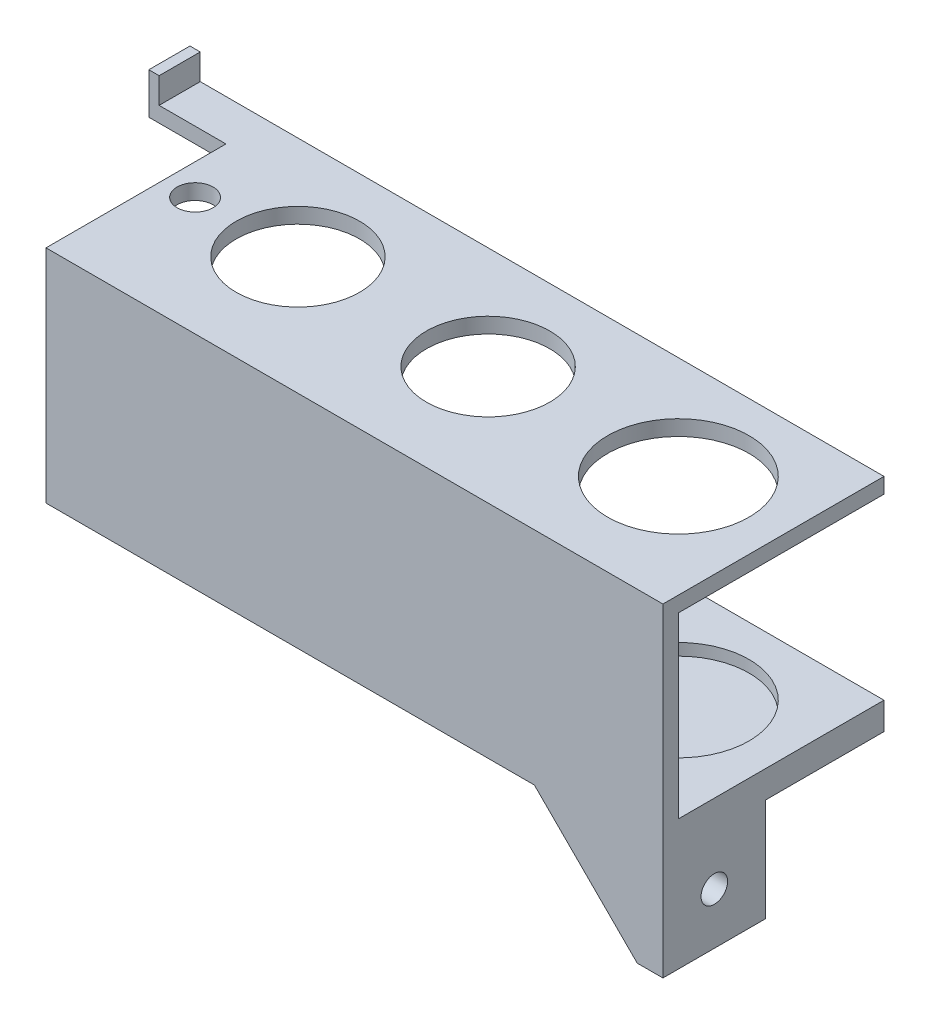
SolidWorks part; units mm, degrees
ref_plane "Front Plane" through (0, 0, 0) normal (0, 0, 1) x (1, 0, 0)
ref_plane "Top Plane" through (0, 0, 0) normal (0, 1, 0) x (1, 0, 0)
ref_plane "Right Plane" through (0, 0, 0) normal (1, 0, 0) x (0, 0, -1)
sketch "Sketch1" plane through (0, 0, 0) normal (1, 0, 0) x (0, 0, -1)
  line L7 (0, -33) -> (3, -33)
  line L8 (3, 7) -> (3, -33)
  line L9 (3, 7) -> (0, 7)
  line L10 (0, 7) -> (0, -33)
  dimension "D4" = 3
  dimension "D5" = 40
extrude "Boss-Extrude1" add sketch "Sketch1" along normal blind 120
sketch "Sketch9" plane through (0, 0, -3) normal (0, 0, -1) x (-1, 0, 0)
  line L0 (0, 7) -> (0, -33) construction
  line L1 (-120, -33) -> (0, -33)
  line L2 (-120, -33) -> (-120, -30)
  line L3 (-120, -30) -> (0, -30)
  line L4 (0, -33) -> (0, -30)
  dimension "D1" = 3
extrude "Boss-Extrude2" add sketch "Sketch9" along normal blind 40
sketch "Sketch10" plane through (0, -30, 0) normal (0, 1, 0) x (1, 0, 0)
  line L0 (120, 43) -> (120, 3) construction
  line L2 (120, 43) -> (0, 43)
  line L3 (120, 43) -> (120, 3)
  line L4 (120, 3) -> (0, 3)
  line L5 (0, 43) -> (0, 3)
  circle A0 centre (100, 23) radius 13.75
  circle A1 centre (63, 23) radius 7.6
  circle A2 centre (26, 23) radius 7.6
  circle A3 centre (6, 23) radius 2.26
  point P5 (120, 23)
  dimension "D1" = 27.5
  dimension "D2" = 20
  dimension "D3" = 15.2
  dimension "D4" = 15.2
  dimension "D5" = 37
  dimension "D6" = 37
  dimension "D7" = 4.52
  dimension "D8" = 20
extrude "Boss-Extrude3" add sketch "Sketch10" along normal blind 2.3
sketch "Sketch11" plane through (0, -30, 0) normal (0, 1, 0) x (1, 0, 0)
  circle A0 centre (63, 23) radius 7
  circle A1 centre (26, 23) radius 2.25
  circle A2 centre (6, 23) radius 2.26
  dimension "D1" = 14
  dimension "D2" = 4.5
extrude "Cut-Extrude5" cut sketch "Sketch11" against normal through all
sketch "Sketch12" plane through (0, 7, 0) normal (0, 1, 0) x (1, 0, 0)
  line L1 (0, 0) -> (120, 0)
  line L2 (0, 0) -> (0, 43)
  line L3 (0, 43) -> (120, 43)
  line L4 (120, 0) -> (120, 43)
  circle A0 centre (6, 23) radius 3.5
  circle A1 centre (26, 23) radius 12
  circle A2 centre (63, 23) radius 12
  circle A3 centre (100, 23) radius 13.75
  circle A4 centre (100, 23) radius 13.75 construction
  dimension "D1" = 24
  dimension "D2" = 24
  dimension "D3" = 7
extrude "Boss-Extrude4" add sketch "Sketch12" along normal blind 3
sketch "Sketch13" plane through (120, 0, 0) normal (1, 0, 0) x (0, 0, -1)
  line L1 (0, -33) -> (20, -33)
  line L2 (0, -33) -> (0, -53)
  line L3 (0, -53) -> (20, -53)
  line L4 (20, -33) -> (20, -53)
  circle A0 centre (10, -43) radius 2.5837
  point P7 (0, 0)
  point P8 (10, -53)
  point P9 (0, 0)
  point P10 (20, -43)
  dimension "D1" = 20
extrude "Boss-Extrude5" add sketch "Sketch13" against normal blind 5
sketch "Sketch14" plane through (0, 0, 0) normal (0, 0, 1) x (1, 0, 0)
  line L0 (115, -53) -> (115, -33)
  line L1 (115, -33) -> (95, -33)
  line L2 (115, -33) -> (0, -33) construction
  line L3 (95, -33) -> (115, -53)
extrude "Boss-Extrude6" add sketch "Sketch14" against normal blind 2
sketch "Sketch15" plane through (0, 10, 0) normal (0, 1, 0) x (1, 0, 0)
  line L1 (0, 43) -> (-15, 43)
  line L2 (0, 43) -> (0, 35)
  line L3 (0, 35) -> (-15, 35)
  line L4 (-15, 43) -> (-15, 35)
  dimension "D1" = 15
  dimension "D2" = 8
extrude "Boss-Extrude7" add sketch "Sketch15" against normal up to surface (3 mm away) up to face at (63, 7, -11)
sketch "Sketch16" plane through (0, 10, 0) normal (0, 1, 0) x (1, 0, 0)
  line L0 (-15, 35) -> (0, 35) construction
  line L1 (-15, 43) -> (-13, 43)
  line L2 (-15, 43) -> (-15, 35)
  line L3 (-15, 35) -> (-13, 35)
  line L4 (-13, 43) -> (-13, 35)
  dimension "D1" = 2
extrude "Boss-Extrude8" add sketch "Sketch16" along normal blind 5
